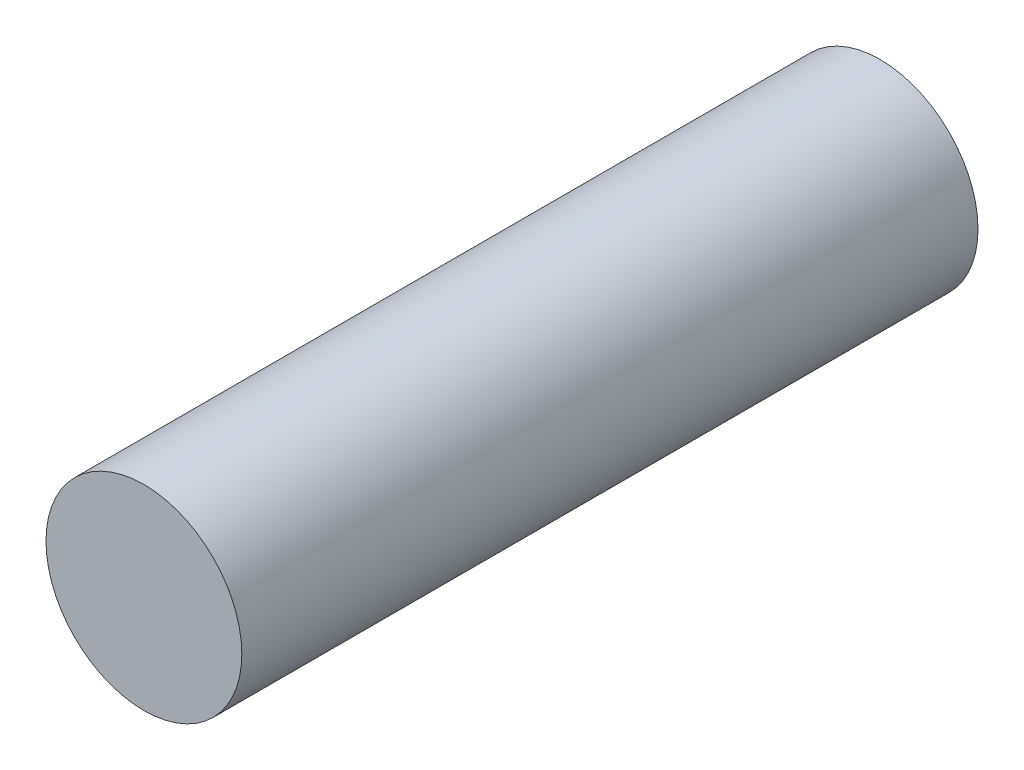
SolidWorks part; units mm, degrees
ref_plane "Front Plane" through (0, 0, 0) normal (0, 0, 1) x (1, 0, 0)
ref_plane "Top Plane" through (0, 0, 0) normal (0, 1, 0) x (1, 0, 0)
ref_plane "Right Plane" through (0, 0, 0) normal (1, 0, 0) x (0, 0, -1)
sketch "Sketch1" plane through (0, 0, 0) normal (0, 0, 1) x (1, 0, 0)
  circle A0 centre (-7.8047, 1.216) radius 3.99
  dimension "D1" = 7.98
extrude "Boss-Extrude1" add sketch "Sketch1" along normal blind 30
